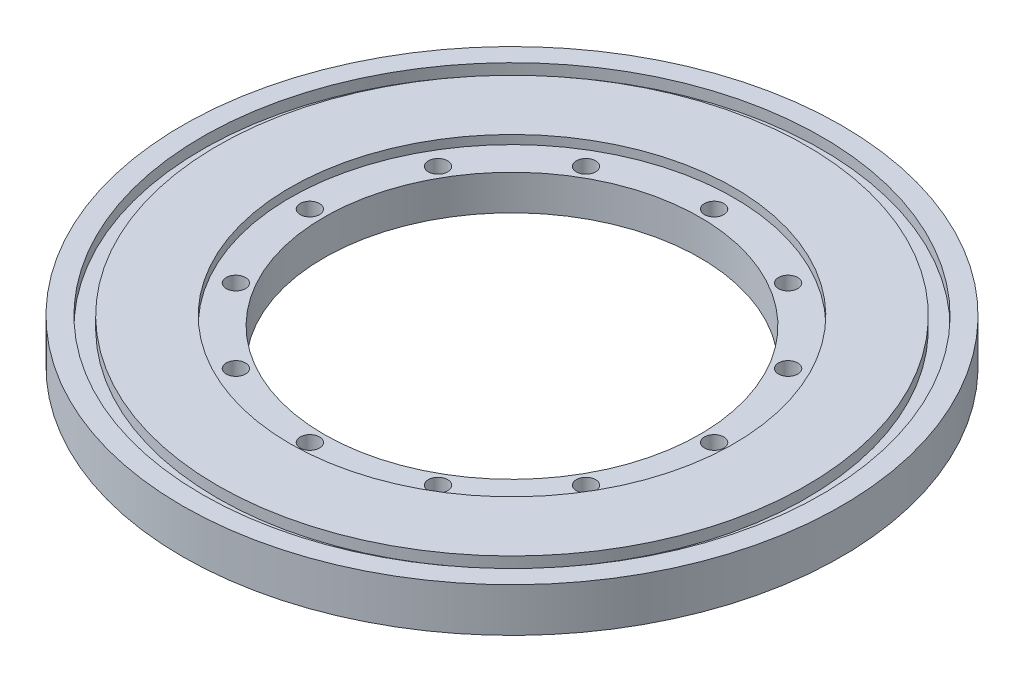
SolidWorks part; units mm, degrees
ref_plane "Front Plane" through (0, 0, 0) normal (0, 0, 1) x (1, 0, 0)
ref_plane "Top Plane" through (0, 0, 0) normal (0, 1, 0) x (1, 0, 0)
ref_plane "Right Plane" through (0, 0, 0) normal (1, 0, 0) x (0, 0, -1)
sketch "Sketch1" plane through (0, 0, 0) normal (0, 1, 0) x (1, 0, 0)
  circle A0 centre (0, 0) radius 95.25
  dimension "D1" = 190.5
extrude "Boss-Extrude1" add sketch "Sketch1" along normal blind 12.7
sketch "Sketch2" plane through (0, 12.7, 0) normal (0, 1, 0) x (1, 0, 0)
  circle A0 centre (0, 0) radius 54.356
  dimension "D1" = 108.712
extrude "Cut-Extrude1" cut sketch "Sketch2" against normal through all
sketch "Sketch3" plane through (0, 12.7, 0) normal (0, 1, 0) x (1, 0, 0)
  circle A0 centre (0, 0) radius 64.135
  dimension "D1" = 128.27
extrude "Cut-Extrude2" cut sketch "Sketch3" against normal blind 2.54
sketch "Sketch4" plane through (0, 12.7, 0) normal (0, 1, 0) x (1, 0, 0)
  circle A0 centre (0, 58.42) radius 2.794
  dimension "D1" = 5.588
  dimension "D2" = 58.42
extrude "Cut-Extrude3" cut sketch "Sketch4" against normal through all
pattern_circular "CirPattern1" count 12 over 360 about axis through (0, 0, 0) along (0, 1, 0) of "Cut-Extrude3"
sketch "Sketch5" plane through (0, 12.7, 0) normal (0, 1, 0) x (1, 0, 0)
  circle A0 centre (0, 0) radius 85.09
  circle A1 centre (0, 0) radius 89.535
  dimension "D1" = 170.18
  dimension "D2" = 179.07
extrude "Cut-Extrude4" cut sketch "Sketch5" against normal blind 3.175
